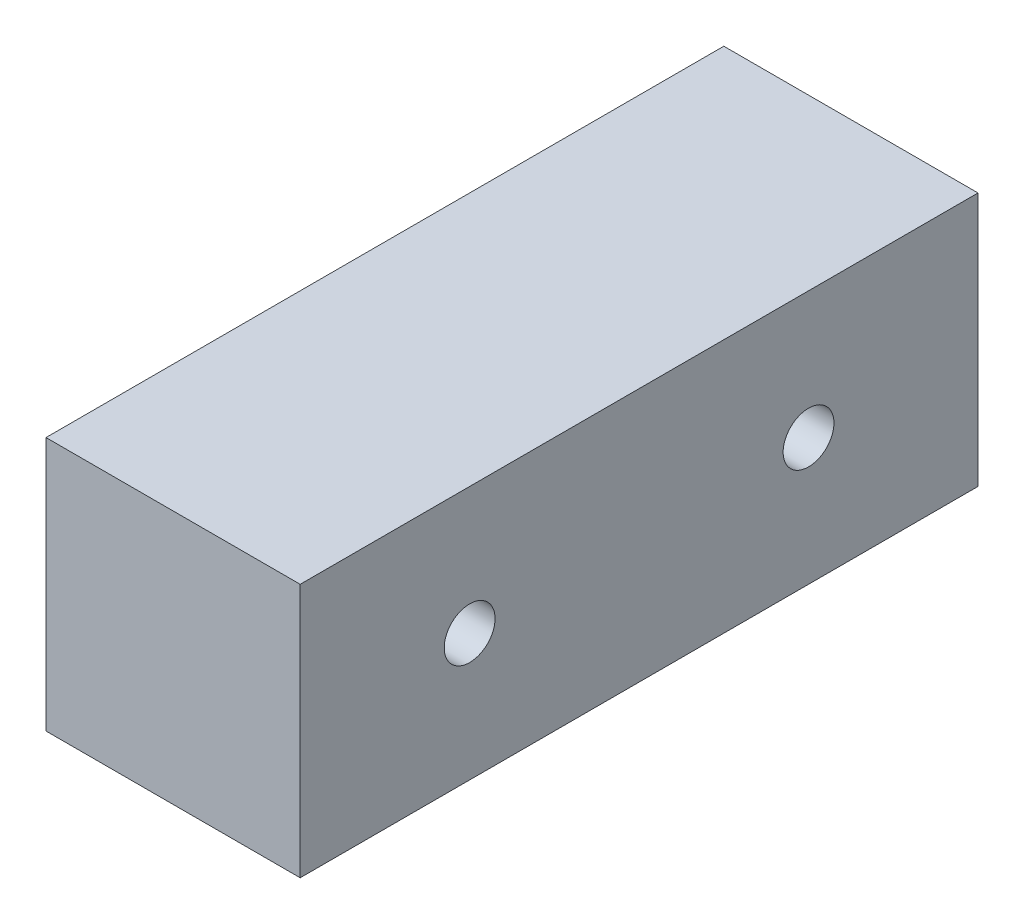
SolidWorks part; units mm, degrees
ref_plane "Front Plane" through (0, 0, 0) normal (0, 0, 1) x (1, 0, 0)
ref_plane "Top Plane" through (0, 0, 0) normal (0, 1, 0) x (1, 0, 0)
ref_plane "Right Plane" through (0, 0, 0) normal (1, 0, 0) x (0, 0, -1)
sketch "Sketch1" plane through (0, 0, 0) normal (0, 1, 0) x (1, 0, 0)
  line L1 (-75, 200) -> (75, 200)
  line L2 (-75, 200) -> (-75, -200)
  line L3 (-75, -200) -> (75, -200)
  line L4 (75, 200) -> (75, -200)
  line L5 (-75, 200) -> (75, -200) construction
  line L6 (-75, -200) -> (75, 200) construction
  point P0 (0, 0)
  dimension "D1" = 150
  dimension "D2" = 400
extrude "Boss-Extrude1" add sketch "Sketch1" along normal blind 150
sketch "Sketch2" plane through (75, 0, 0) normal (1, 0, 0) x (0, 0, -1)
  line L0 (-200, 0) -> (200, 0) construction
  line L1 (-200, 150) -> (-200, 0) construction
  line L2 (200, 150) -> (200, 0) construction
  circle A0 centre (-100, 75) radius 15
  circle A1 centre (100, 75) radius 15
  dimension "D1" = 30
  dimension "D2" = 75
  dimension "D3" = 100
  dimension "D4" = 30
  dimension "D5" = 75
  dimension "D6" = 100
extrude "Cut-Extrude1" cut sketch "Sketch2" against normal through all
